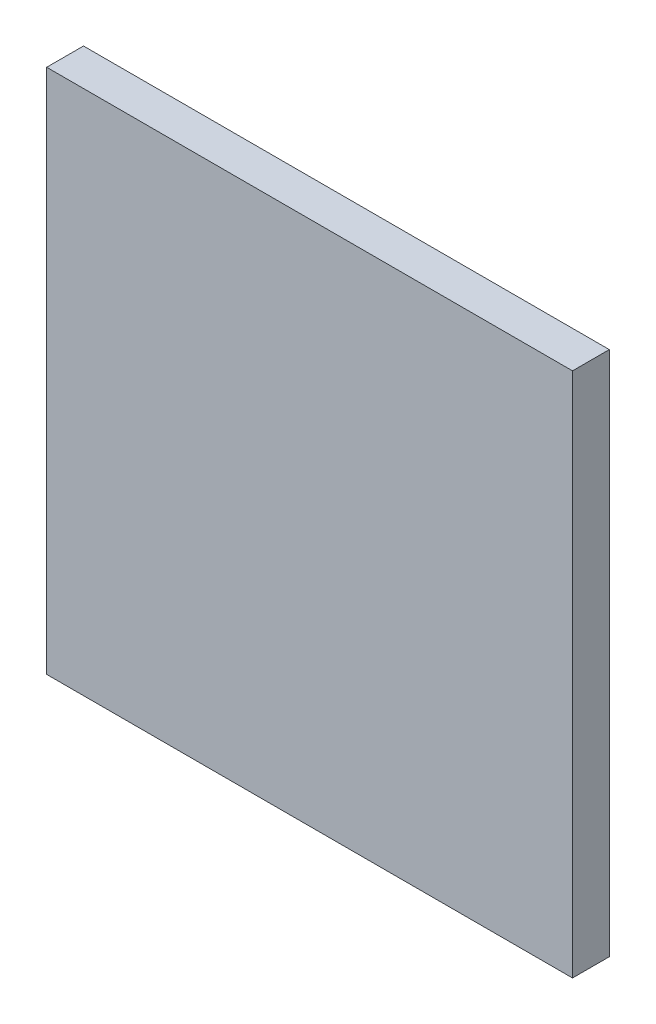
SolidWorks part; units mm, degrees
material "Латунь"
ref_plane "Спереди" through (0, 0, 0) normal (0, 0, 1) x (1, 0, 0)
ref_plane "Сверху" through (0, 0, 0) normal (0, 1, 0) x (1, 0, 0)
ref_plane "Справа" through (0, 0, 0) normal (1, 0, 0) x (0, 0, -1)
sketch "Эскиз1" plane through (0, 0, 0) normal (0, 0, 1) x (1, 0, 0)
  line L1 (-25, 25) -> (25, 25)
  line L2 (-25, 25) -> (-25, -25)
  line L3 (-25, -25) -> (25, -25)
  line L4 (25, 25) -> (25, -25)
  line L5 (-25, 25) -> (25, -25) construction
  line L6 (-25, -25) -> (25, 25) construction
  point P0 (0, 0)
  dimension "D1" = 50
  dimension "D2" = 50
extrude "Бобышка-Вытянуть1" add sketch "Эскиз1" along normal blind 3.5
